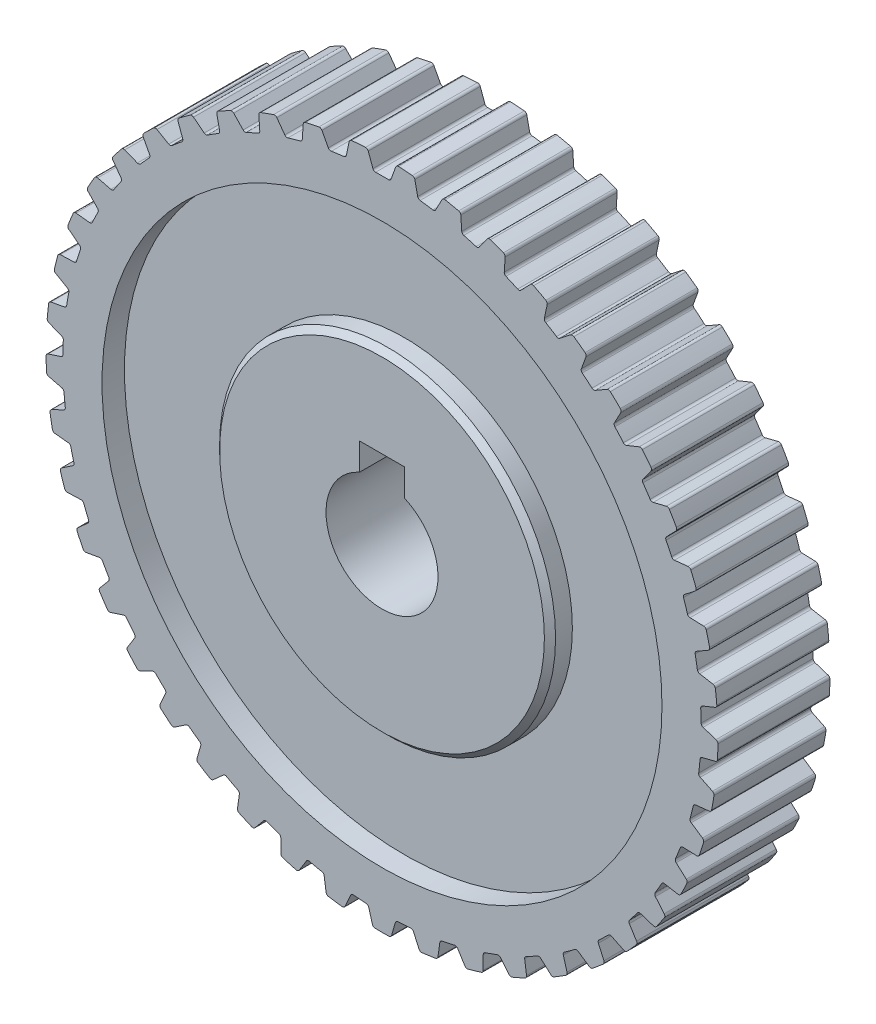
SolidWorks part; units mm, degrees
ref_plane "Front Plane" through (0, 0, 0) normal (0, 0, 1) x (1, 0, 0)
ref_plane "Top Plane" through (0, 0, 0) normal (0, 1, 0) x (1, 0, 0)
ref_plane "Right Plane" through (0, 0, 0) normal (1, 0, 0) x (0, 0, -1)
sketch "Sketch2" plane through (0, 0, 0) normal (0, 0, 1) x (1, 0, 0)
  line L0 (0, 0) -> (0, 49.3358) construction
  line L2 (-2, 7) -> (2, 7)
  line L3 (-2, 7) -> (-2, 4.5826)
  line L5 (2, 7) -> (2, 4.5826)
  arc A0 (-2, 4.5826) -> (2, 4.5826) centre (0, 0) ccw
  circle A1 centre (0, 0) radius 30
  dimension "D1" = 60
  dimension "D2" = 10
  dimension "D3" = 4
  dimension "D4" = 7
extrude "Boss-Extrude1" add sketch "Sketch2" along normal mid plane 10
sketch "Sketch3" plane through (0, 0, 5) normal (0, 0, 1) x (1, 0, 0)
  line L0 (0, 0) -> (0, 51.6905) construction
  line L2 (0.75, 28.4901) -> (1.2895, 29.9723)
  line L3 (-0.75, 28.4901) -> (-1.2895, 29.9723)
  circle A0 centre (0, 0) radius 30 construction
  circle A1 centre (0, 0) radius 30
  arc A2 (-0.75, 28.4901) -> (0.75, 28.4901) centre (0, 0) cw
  point P9 (0, 28.5)
  point P10 (0, 0)
  dimension "D1" = 1.5
  dimension "D2" = 20
  dimension "D3" = 20
  dimension "D4" = 28.5
extrude "Cut-Extrude1" cut sketch "Sketch3" against normal through all
pattern_circular "CirPattern1" count 45 over 360 about axis through (0, 0, 0) along (0, 0, 1) of "Cut-Extrude1"
sketch "Sketch4" plane through (0, 0, 5) normal (0, 0, 1) x (1, 0, 0)
  circle A0 centre (0, 0) radius 25
  dimension "D1" = 50
extrude "Cut-Extrude-Thin1" cut sketch "Sketch4" against normal blind 2 thin thin type one direction reverse wall 10
chamfer "Chamfer1" distance 0.5 angle 45 1 edges at (15, 0, 5)
mirror "Mirror2" about plane through (0, 0, 0) normal (0, 0, 1) of "Cut-Extrude-Thin1"
chamfer "Chamfer2" distance 0.5 angle 45 1 edges at (15, 0, -5)
fillet "Fillet1" radius 0.25 110 edges at (29.9429, -1.8506, 0) (29.999, -0.2427, 0) (28.4989, 0.2447, 0) (28.4466, 1.7438, 0) (29.909, 2.3347, 0) (27.9271, 5.6859, 0) (27.3275, 8.0906, 0) (28.1069, 10.4883, 0) (27.5042, 11.98, 0) (25.9355, 11.8152, 0) (23.1366, 19.0971, 0) (21.6741, 18.5063, 0) (20.6704, 19.621, 0) (21.4109, 21.0136, 0) (20.2536, 22.1312, 0) (18.278, 23.7889, 0) (15.7335, 23.7636, 0) (14.4614, 24.5584, 0) (14.7894, 26.1012, 0) (13.3688, 26.8566, 0) (10.9028, 26.3321, 0) (11.0128, 27.9055, 0) (9.501, 28.4558, 0) (7.022, 29.1666, 0) (3.2224, 28.3172, 0) (0.75, 28.4901, 0) (-0.75, 28.4901, 0) (-1.2895, 29.9723, 0) (-2.8944, 29.86, 0) (-4.7078, 28.1085, 0) (-5.4482, 29.5011, 0) (-11.0128, 27.9055, 0) (-10.9028, 26.3321, 0) (-12.2731, 25.722, 0) (-13.3688, 26.8566, 0) (-14.7894, 26.1012, 0) (-14.4614, 24.5584, 0) (-15.7335, 23.7636, 0) (-17.7386, 22.3068, 0) (-21.4109, 21.0136, 0) (-20.6704, 19.621, 0) (-21.6741, 18.5063, 0) (-23.1366, 19.0971, 0) (-24.1271, 17.8293, 0) (-23.2, 16.5533, 0) (-24.0388, 15.3097, 0) (-25.5692, 15.6913, 0) (-25.9355, 11.8152, 0) (-28.1069, 10.4883, 0) (-26.864, 9.5172, 0) (-27.3275, 8.0906, 0) (-28.9038, 8.0356, 0) (-27.9271, 5.6859, 0) (-28.1875, 4.2087, 0) (-29.7408, 3.9348, 0) (-28.4466, 1.7438, 0) (-29.999, -0.2427, 0) (-29.9429, -1.8506, 0) (-28.4125, -2.2321, 0) (-29.6733, -4.4153, 0) (-27.8253, -6.1647, 0) (-27.4624, -7.6201, 0) (-28.77, -8.5021, 0) (-28.2728, -10.0322, 0) (-26.6965, -9.9772, 0) (-27.3068, -12.4234, 0) (-25.0482, -13.5955, 0) (-24.2982, -14.8946, 0) (-25.312, -16.1028, 0) (-24.4123, -17.4367, 0) (-22.9123, -16.9493, 0) (-21.9888, -18.1313, 0) (-21.748, -20.6645, 0) (-20.3304, -19.9731, 0) (-19.2514, -21.0151, 0) (-16.1393, -23.4898, 0) (-16.5741, -25.006, 0) (-15.2097, -25.8586, 0) (-14.0375, -24.8032, 0) (-12.7131, -25.5074, 0) (-9.0394, -27.0285, 0) (-7.4929, -29.0492, 0) (-4.9703, -29.5854, 0) (-0.8044, -29.9892, 0) (0.8044, -29.9892, 0) (1.2392, -28.473, 0) (2.7355, -28.3684, 0) (3.3771, -29.8093, 0) (4.9703, -29.5854, 0) (5.1898, -28.0235, 0) (6.657, -27.7116, 0) (9.0394, -28.6057, 0) (9.0394, -27.0285, 0) (10.449, -26.5154, 0) (15.2097, -25.8586, 0) (17.3528, -22.6082, 0) (19.2514, -21.0151, 0) (20.3304, -19.9731, 0) (22.9123, -16.9493, 0) (25.312, -16.1028, 0) (24.2982, -14.8946, 0) (25.0482, -13.5955, 0) (26.6015, -13.8694, 0) (27.3068, -12.4234, 0) (26.1346, -11.368, 0) (26.6965, -9.9772, 0) (28.2728, -10.0322, 0) (29.3939, -5.9998, 0) (29.6733, -4.4153, 0) (28.4125, -2.2321, 0)
